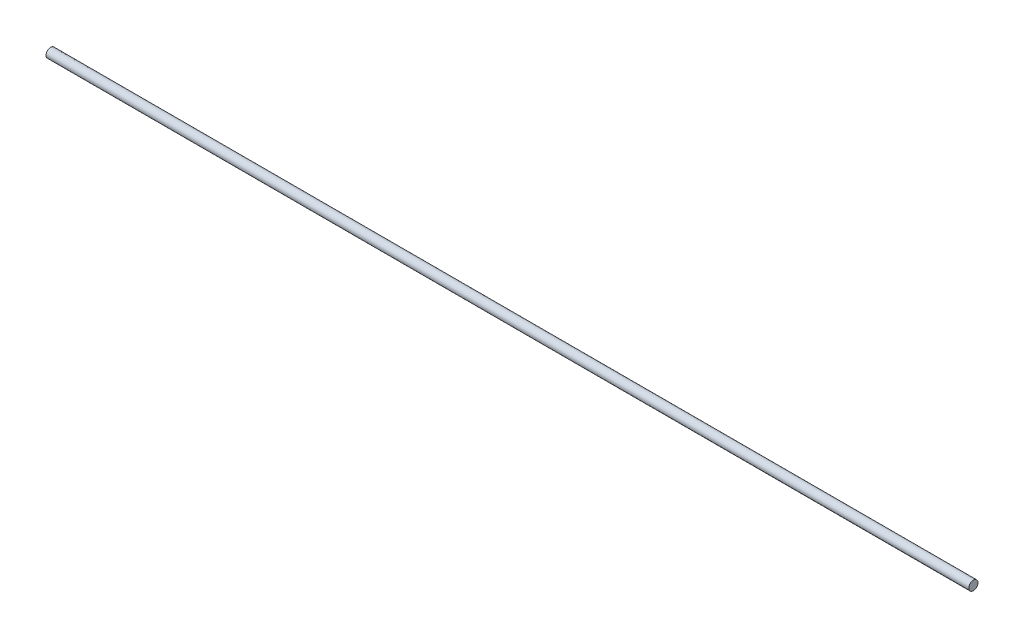
SolidWorks part; units mm, degrees
ref_plane "Alzado" through (0, 0, 0) normal (0, 0, 1) x (1, 0, 0)
ref_plane "Planta" through (0, 0, 0) normal (0, 1, 0) x (1, 0, 0)
ref_plane "Vista lateral" through (0, 0, 0) normal (1, 0, 0) x (0, 0, -1)
sketch "Croquis1" plane through (0, 0, 0) normal (1, 0, 0) x (0, 0, -1)
  circle A0 centre (0, 0) radius 4
  dimension "D1" = 8
extrude "Saliente-Extruir1" add sketch "Croquis1" along normal blind 800
